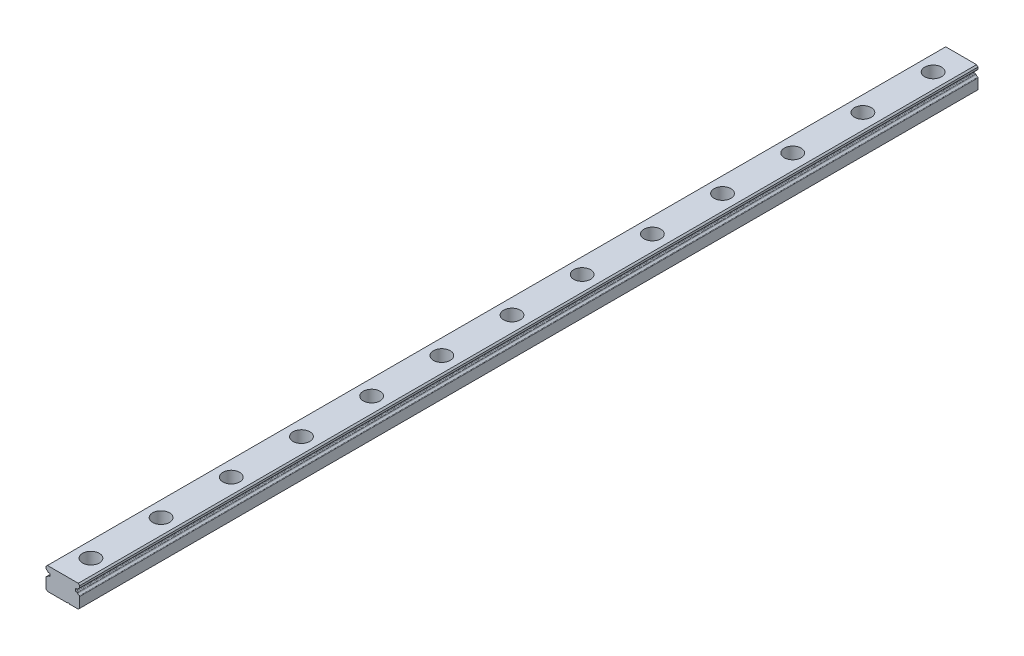
SolidWorks part; units mm, degrees
ref_plane "Front Plane" through (0, 0, 0) normal (0, 0, 1) x (1, 0, 0)
ref_plane "Top Plane" through (0, 0, 0) normal (0, 1, 0) x (1, 0, 0)
ref_plane "Right Plane" through (0, 0, 0) normal (1, 0, 0) x (0, 0, -1)
sketch "Sketch1" plane through (0, 0, 0) normal (0, 0, 1) x (1, 0, 0)
  line L0 (-6, 0) -> (6, 0) construction
  line L1 (0, -4) -> (0, 4) construction
  line L2 (0, 4) -> (0, -4) construction
  line L3 (-3, 4) -> (3, 4) construction
  line L4 (-1.75, -0.5) -> (1.75, -0.5) construction
  point P0 (0, -0.5)
  point P3 (-6, -4)
  point P4 (0, 0)
  point P8 (0, 0)
  point P11 (0, 4)
  point P15 (0, 4)
  point P17 (0, -0.5)
  point P18 (6, 4)
  point P20 (-6, 4)
  dimension "Rail Width" = 12
  dimension "Rail Height" = 8
  dimension "Mounting Hole Depth" = 3.5
  dimension "Mounting Hole Counterbore Diameter" = 6
  dimension "Mounting Hole Diameter" = 3.5
sketch "Sketch2" plane through (0, 0, 0) normal (1, 0, 0) x (0, 0, -1)
  line L0 (160, 0) -> (-160, 0) construction
  line L1 (-6.5, 4) -> (6.5, 4) construction
  line L3 (0, 4) -> (0, 0) construction
  point P0 (-150, 0)
  point P4 (0, 0)
  point P5 (-125, 0)
  point P6 (-137.5, 0)
  point P9 (-150, 4)
  point P10 (0, 4)
  point P11 (160, 4)
  point P13 (-160, 4)
  point P14 (137.5, 0)
  point P17 (-160, -4)
  dimension "Rail Length" = 320
  dimension "Mounting Hole Center to Edge" = 10
  dimension "Mounting Hole Center to Center" = 25
  dimension "Number of Mounting Holes" = 13
  dimension "Break Line" = 12.5
sketch "Sketch3" plane through (0, 0, 0) normal (0, 0, 1) x (1, 0, 0)
  point P0 (0, 4)
  line B0 (-6, 0.1421) -> (-6, -3.5)
  line B1 (-6, -3.5) -> (-5.5, -4)
  line B2 (-5.5, -4) -> (1.6, -4)
  line B3 (2.4, -4) -> (5.5, -4)
  line B4 (5.5, -4) -> (6, -3.5)
  line B5 (6, -3.5) -> (6, 0.1421)
  line B6 (5.0738, 0.9945) -> (4.7282, 1.0247)
  line B7 (4.5, 1.2738) -> (4.5, 1.7262)
  line B8 (4.7282, 1.9753) -> (5.0948, 2.0073)
  line B9 (6, 2.8254) -> (6, 3.5)
  line B10 (6, 3.5) -> (5.5, 4)
  line B11 (5.5, 4) -> (-5.5, 4)
  line B12 (-5.5, 4) -> (-6, 3.5)
  line B13 (-6, 3.5) -> (-6, 2.8254)
  line B14 (-5.0948, 2.0073) -> (-4.7282, 1.9753)
  line B15 (-4.5, 1.7262) -> (-4.5, 1.2738)
  line B16 (-4.7282, 1.0247) -> (-5.0738, 0.9945)
  arc B17 (-5.8448, 0.3734) -> (-6, 0.1421) centre (-5.75, 0.1421) ccw
  arc B18 (2.4, -4) -> (1.6, -4) centre (2, -4.3) ccw
  arc B19 (6, 0.1421) -> (5.8448, 0.3734) centre (5.75, 0.1421) ccw
  arc B20 (5.2672, 0.8728) -> (5.8448, 0.3734) centre (6.3, 1.4838) ccw
  arc B21 (5.2672, 0.8728) -> (5.0738, 0.9945) centre (5.052, 0.7455) ccw
  arc B22 (4.5, 1.2738) -> (4.7282, 1.0247) centre (4.75, 1.2738) ccw
  arc B23 (4.7282, 1.9753) -> (4.5, 1.7262) centre (4.75, 1.7262) ccw
  arc B24 (5.0948, 2.0073) -> (5.2845, 2.1232) centre (5.073, 2.2564) ccw
  arc B25 (5.8448, 2.5941) -> (5.2845, 2.1232) centre (6.3, 1.4838) ccw
  arc B26 (5.8448, 2.5941) -> (6, 2.8254) centre (5.75, 2.8254) ccw
  arc B27 (-6, 2.8254) -> (-5.8448, 2.5941) centre (-5.75, 2.8254) ccw
  arc B28 (-5.2845, 2.1232) -> (-5.8448, 2.5941) centre (-6.3, 1.4838) ccw
  arc B29 (-5.2845, 2.1232) -> (-5.0948, 2.0073) centre (-5.073, 2.2564) ccw
  arc B30 (-4.5, 1.7262) -> (-4.7282, 1.9753) centre (-4.75, 1.7262) ccw
  arc B31 (-4.7282, 1.0247) -> (-4.5, 1.2738) centre (-4.75, 1.2738) ccw
  arc B32 (-5.0738, 0.9945) -> (-5.2672, 0.8728) centre (-5.052, 0.7455) ccw
  arc B33 (-5.8448, 0.3734) -> (-5.2672, 0.8728) centre (-6.3, 1.4838) ccw
sketch_block_instance "12mm Block-1"
sketch_block "12mm Block"
extrude "Boss-Extrude1" add sketch "Sketch3" against normal up to vertex (160 mm away) from vertex at 160 starting at point (0, 0, 160)
ref_plane "Plane1" through (0, 0, 150) normal (0, 0, 1) x (1, 0, 0)
sketch "Sketch4" plane through (0, 0, 150) normal (0, 0, 1) x (1, 0, 0)
  line L0 (0, 4) -> (0, -4)
  line L1 (0, -4) -> (-1.75, -4)
  line L3 (-1.75, -4) -> (-1.75, -0.5)
  line L4 (-1.75, -0.5) -> (-3, -0.5)
  line L5 (-3, -0.5) -> (-3, 4)
  line L6 (-3, 4) -> (0, 4)
revolve "Cut-Revolve1" cut sketch "Sketch4" angle 360 about L0
sketch "Sketch6" plane through (0, 0, 0) normal (1, 0, 0) x (0, 0, -1)
  line L0 (-147, -0.5) -> (-153, -0.5) construction
  line L5 (-147, -0.5) -> (-153, -0.5)
  line L17 (-151.75, -0.5) -> (-151.75, -4) construction
  line L18 (-148.25, -4) -> (-148.25, -0.5) construction
  line L32 (-147, -0.5) -> (-147, 4) construction
  line L33 (-153, 4) -> (-153, -0.5) construction
  line L34 (-151.75, -0.5) -> (-151.75, -4)
  line L35 (-148.25, -4) -> (-148.25, -0.5)
  line L36 (-147, -0.5) -> (-147, 4)
  line L37 (-153, 4) -> (-153, -0.5)
  line L38 (0, 4) -> (0, -4) construction
  line L40 (153, 4) -> (153, -0.5)
  line L41 (147, -0.5) -> (147, 4)
  line L42 (148.25, -4) -> (148.25, -0.5)
  line L43 (151.75, -0.5) -> (151.75, -4)
  line L44 (147, -0.5) -> (153, -0.5)
sketch "Sketch7" plane through (0, 0, 0) normal (0, 0, 1) x (1, 0, 0)
  line L0 (3, -0.5) -> (3, 4) construction
  line L1 (-3, 4) -> (-3, -0.5) construction
  line L2 (3, -0.5) -> (3, 4)
  line L3 (-3, 4) -> (-3, -0.5)
  line L4 (1.75, -3.867) -> (1.75, -0.5) construction
  line L11 (1.75, -3.867) -> (1.75, -0.5)
  line L18 (-1.75, -0.5) -> (-1.75, -4) construction
  line L32 (3, -0.5) -> (-3, -0.5) construction
  line L34 (-1.75, -0.5) -> (-1.75, -4)
  line L37 (3, -0.5) -> (-3, -0.5)
pattern_linear "LPattern1" count 13 spacing 25 along (0, 0, -1) of "Cut-Revolve1"
equation "\"D3@LPattern1\"=\"Mounting Hole Center to Center@Sketch2\""
equation "\"D1@LPattern1\"=\"Number of Mounting Holes@Sketch2\""
equation "\"Break Line@Sketch2\"=\"Mounting Hole Center to Center@Sketch2\"/2"
